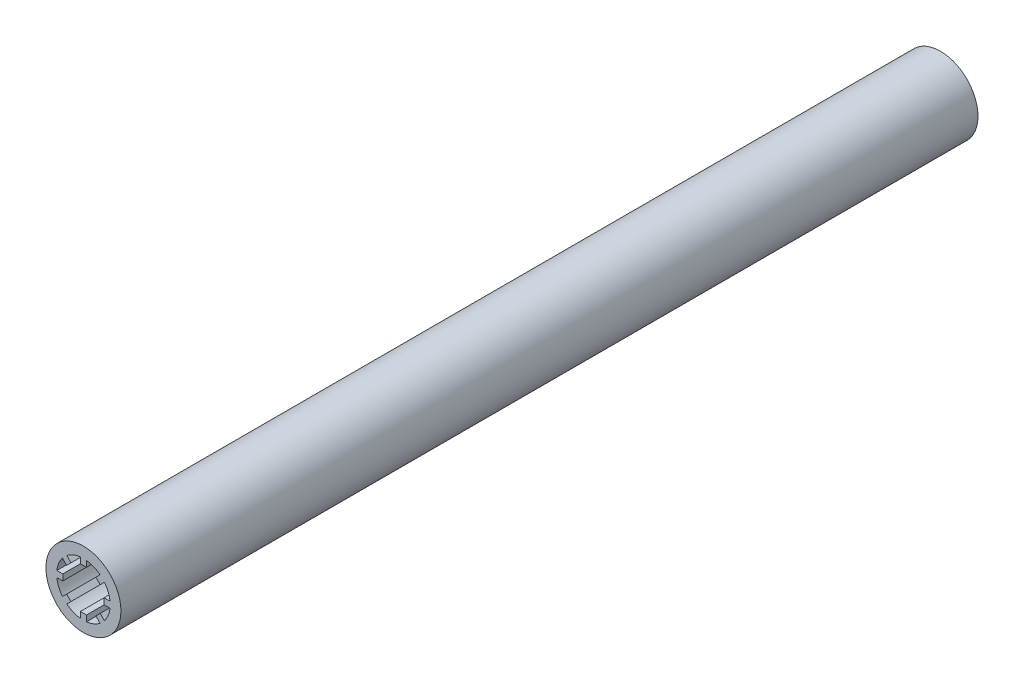
SolidWorks part; units mm, degrees
ref_plane "Front Plane" through (0, 0, 0) normal (0, 0, 1) x (1, 0, 0)
ref_plane "Top Plane" through (0, 0, 0) normal (0, 1, 0) x (1, 0, 0)
ref_plane "Right Plane" through (0, 0, 0) normal (1, 0, 0) x (0, 0, -1)
sketch "Sketch1" plane through (0, 0, 0) normal (0, 0, 1) x (1, 0, 0)
  circle A0 centre (0, 0) radius 12.25
  dimension "D1" = 24.5
extrude "Boss-Extrude1" add sketch "Sketch1" along normal blind 280
sketch "Sketch2" plane through (0, 0, 280) normal (0, 0, 1) x (1, 0, 0)
  line L2 (1, 6.75) -> (-1, 6.75)
  line L3 (-1, 8.6927) -> (-1, 6.75)
  line L4 (1, 8.6927) -> (1, 6.75)
  line L5 (5.4395, 6.8538) -> (4.0659, 5.4801)
  line L6 (5.4801, 4.0659) -> (4.0659, 5.4801)
  line L7 (6.8538, 5.4395) -> (5.4801, 4.0659)
  line L8 (8.6927, 1) -> (6.75, 1)
  line L9 (6.75, -1) -> (6.75, 1)
  line L10 (8.6927, -1) -> (6.75, -1)
  line L11 (6.8538, -5.4395) -> (5.4801, -4.0659)
  line L12 (4.0659, -5.4801) -> (5.4801, -4.0659)
  line L13 (5.4395, -6.8538) -> (4.0659, -5.4801)
  line L14 (1, -8.6927) -> (1, -6.75)
  line L15 (-1, -6.75) -> (1, -6.75)
  line L16 (-1, -8.6927) -> (-1, -6.75)
  line L17 (-5.4395, -6.8538) -> (-4.0659, -5.4801)
  line L18 (-5.4801, -4.0659) -> (-4.0659, -5.4801)
  line L19 (-6.8538, -5.4395) -> (-5.4801, -4.0659)
  line L20 (-8.6927, -1) -> (-6.75, -1)
  line L21 (-6.75, 1) -> (-6.75, -1)
  line L22 (-8.6927, 1) -> (-6.75, 1)
  line L23 (-6.8538, 5.4395) -> (-5.4801, 4.0659)
  line L24 (-4.0659, 5.4801) -> (-5.4801, 4.0659)
  line L25 (-5.4395, 6.8538) -> (-4.0659, 5.4801)
  arc A0 (-1, 8.6927) -> (-5.4395, 6.8538) centre (0, 0) ccw
  arc A1 (5.4395, 6.8538) -> (1, 8.6927) centre (0, 0) ccw
  arc A2 (8.6927, 1) -> (6.8538, 5.4395) centre (0, 0) ccw
  arc A3 (6.8538, -5.4395) -> (8.6927, -1) centre (0, 0) ccw
  arc A4 (1, -8.6927) -> (5.4395, -6.8538) centre (0, 0) ccw
  arc A5 (-5.4395, -6.8538) -> (-1, -8.6927) centre (0, 0) ccw
  arc A6 (-8.6927, -1) -> (-6.8538, -5.4395) centre (0, 0) ccw
  arc A7 (-6.8538, 5.4395) -> (-8.6927, 1) centre (0, 0) ccw
  point P37 (0, 0)
  dimension "D1" = 17.5
  dimension "D2" = 8
extrude "Cut-Extrude1" cut sketch "Sketch2" against normal blind 20
